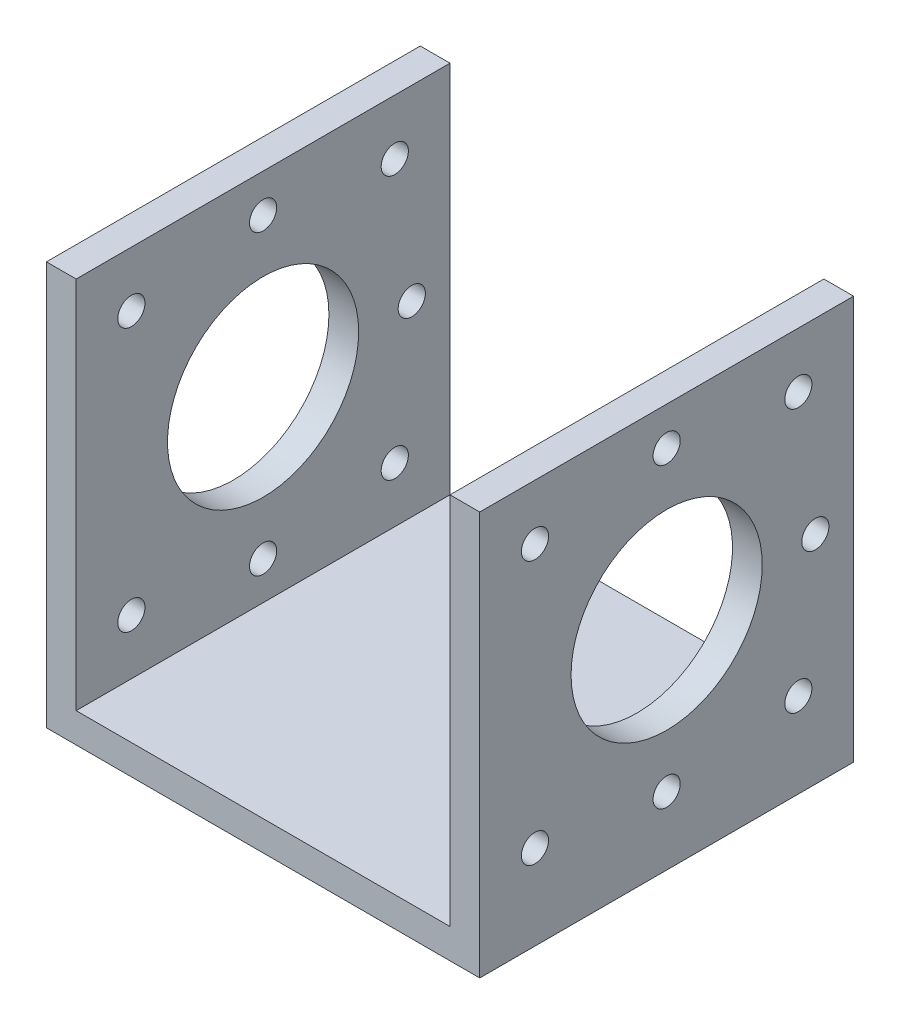
SolidWorks part; units mm, degrees
ref_plane "Front Plane" through (0, 0, 0) normal (0, 0, 1) x (1, 0, 0)
ref_plane "Top Plane" through (0, 0, 0) normal (0, 1, 0) x (1, 0, 0)
ref_plane "Right Plane" through (0, 0, 0) normal (1, 0, 0) x (0, 0, -1)
sketch "Sketch1" plane through (0, 0, 0) normal (0, 1, 0) x (1, 0, 0)
  line L1 (-22, -22) -> (22, -22)
  line L2 (-22, -22) -> (-22, 22)
  line L3 (-22, 22) -> (22, 22)
  line L4 (22, -22) -> (22, 22)
  line L5 (-22, -22) -> (22, 22) construction
  line L6 (-22, 22) -> (22, -22) construction
  point P0 (0, 0)
  dimension "D1" = 44
  dimension "D2" = 44
extrude "Boss-Extrude1" add sketch "Sketch1" against normal blind 3.5
sketch "Sketch3" plane through (0, 0, 0) normal (0, 1, 0) x (1, 0, 0)
  line L1 (22, -22) -> (25.5, -22)
  line L2 (22, -22) -> (22, 22)
  line L3 (22, 22) -> (25.5, 22)
  line L4 (25.5, -22) -> (25.5, 22)
  dimension "D1" = 3.5
extrude "Boss-Extrude2" add sketch "Sketch3" along normal blind 44 and the other way blind 3.5
sketch "Sketch4" plane through (0, 0, 0) normal (0, 1, 0) x (1, 0, 0)
  line L1 (-22, 22) -> (-25.5, 22)
  line L2 (-22, 22) -> (-22, -22)
  line L3 (-22, -22) -> (-25.5, -22)
  line L4 (-25.5, 22) -> (-25.5, -22)
  dimension "D1" = 3.5
extrude "Boss-Extrude3" add sketch "Sketch4" along normal blind 44 and the other way blind 3.5
sketch "Sketch5" plane through (0, 0, 0) normal (1, 0, 0) x (0, 0, -1)
  line L0 (22, 44) -> (-22, 44) construction
  circle A0 centre (0, 22) radius 11.25
  dimension "D1" = 22.5
  dimension "D2" = 22
extrude "Cut-Extrude1" cut sketch "Sketch5" along normal through all both and the other way through all contours A0
sketch "Sketch11" plane through (25.5, 0, 0) normal (1, 0, 0) x (0, 0, -1)
  line L0 (-15.5, 44) -> (-15.5, -3.5) construction
  line L1 (-22, 44) -> (22, 44) construction
  line L2 (-22, -3.5) -> (22, -3.5) construction
  line L3 (-22, -3.5) -> (-22, 44) construction
  line L4 (-22, 37.5) -> (22, 37.5) construction
  line L5 (22, -3.5) -> (22, 44) construction
  line L6 (15.5, 44) -> (15.5, -3.5) construction
  line L8 (-22, 6.5) -> (22, 6.5) construction
  point P14 (-15.5, 37.5)
  point P23 (15.5, 37.5)
  point P25 (15.5, 6.5)
  point P27 (-15.5, 6.5)
  dimension "D1" = 6.5
  dimension "D2" = 6.5
  dimension "D3" = 6.5
  dimension "D4" = 10
hole_wizard "M3 Clearance Hole1" positions "Sketch11" profile "Sketch12" hole size "M3" standard "ANSI Metric" end condition through all
sketch "Sketch12" plane through (25.5, 6.5, 15.5) normal (0, 1, 0) x (0, 0, -1)
  line L0 (0, 0) -> (0, 51)
  line L1 (0, 51) -> (1.6, 51)
  line L2 (1.6, 51) -> (1.6, 0)
  line L5 (1.6, 0) -> (0, 0)
  line L11 (0, -6.35) -> (0, 107.95) construction
  dimension "Thru Hole Dia." = 3.2
  dimension "Thru Hole Depth" = 51
sketch "Sketch15" plane through (0, 0, 0) normal (1, 0, 0) x (0, 0, -1)
  circle A0 centre (0, 22) radius 17.5 construction
  point P5 (0, 39.5)
  point P9 (0, 4.5)
  point P12 (17.5, 22)
  dimension "D1" = 35
hole_wizard "M3 Clearance Hole2" positions "Sketch15" profile "Sketch16" hole size "M3" standard "ANSI Metric"
sketch "Sketch16" plane through (0, 22, -17.5) normal (0, 1, 0) x (0, 0, 1)
  line L0 (0, 0) -> (0, 25.5)
  line L1 (0, 25.5) -> (1.6, 25.5)
  line L2 (1.6, 25.5) -> (1.6, 0)
  line L5 (1.6, 0) -> (0, 0)
  line L11 (0, -6.35) -> (0, 107.95) construction
  dimension "Thru Hole Dia." = 3.2
  dimension "Thru Hole Depth" = 25.5
sketch "Sketch17" plane through (-25.5, 0, 0) normal (-1, 0, 0) x (0, 0, 1)
  circle A0 centre (0, 22) radius 17.5 construction
  point P4 (0, 39.5)
  point P6 (-17.5, 22)
  point P8 (0, 4.5)
  dimension "D1" = 35
hole_wizard "M3 Clearance Hole3" positions "Sketch17" profile "Sketch18" hole size "M3" standard "ANSI Metric" end condition through all
sketch "Sketch18" plane through (-25.5, 4.5, 0) normal (0, 1, 0) x (0, 0, 1)
  line L0 (0, 0) -> (0, 51)
  line L1 (0, 51) -> (1.6, 51)
  line L2 (1.6, 51) -> (1.6, 0)
  line L5 (1.6, 0) -> (0, 0)
  line L11 (0, -6.35) -> (0, 107.95) construction
  dimension "Thru Hole Dia." = 3.2
  dimension "Thru Hole Depth" = 51
